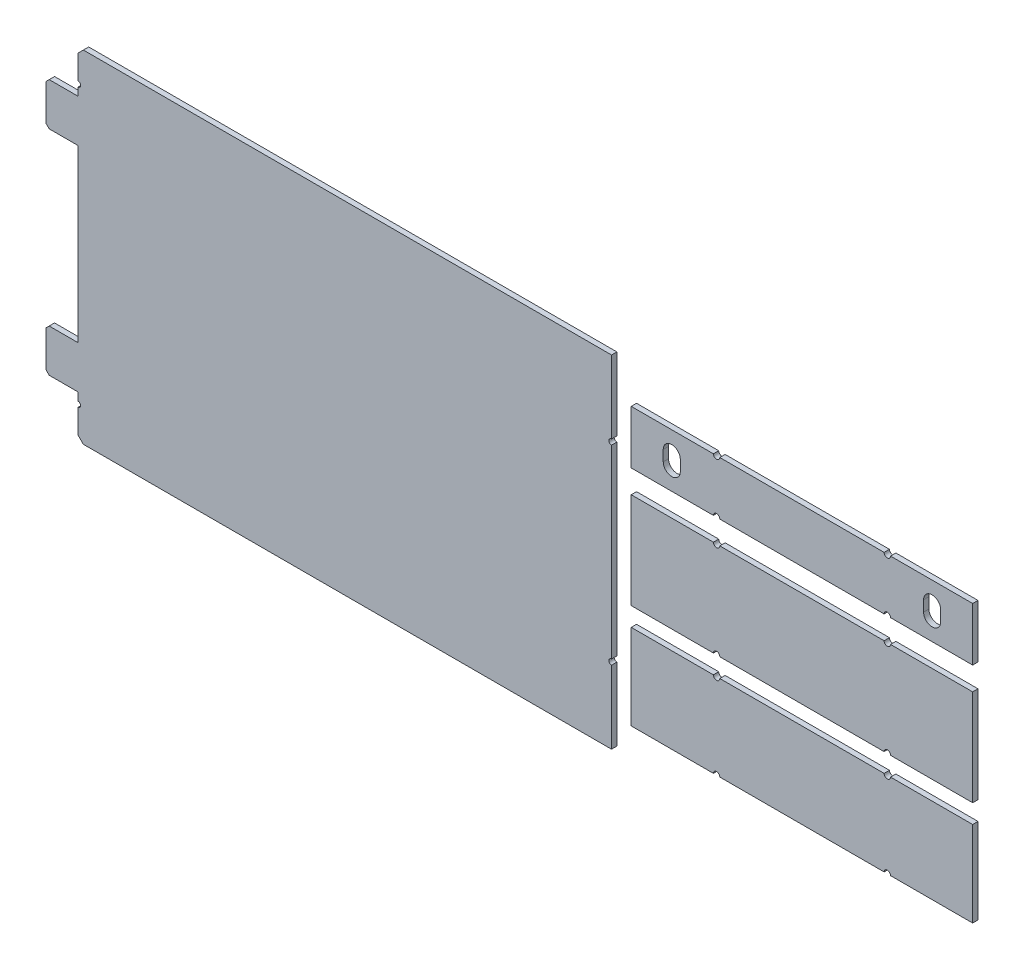
SolidWorks part; units mm, degrees
ref_plane "Ön Düzlem" through (0, 0, 0) normal (0, 0, 1) x (1, 0, 0)
ref_plane "Üst Düzlem" through (0, 0, 0) normal (0, 1, 0) x (1, 0, 0)
ref_plane "Sağ Düzlem" through (0, 0, 0) normal (1, 0, 0) x (0, 0, -1)
sketch "Çizim1" plane through (0, 0, 0) normal (0, 0, 1) x (1, 0, 0)
  line L0 (1992.452, 1746.7533) -> (1992.452, 1712.7533)
  line L1 (1995.452, 1709.7533) -> (2022.452, 1709.7533)
  line L2 (1992.452, 1712.7533) -> (1995.452, 1709.7533)
  line L3 (1995.452, 1749.7533) -> (2022.452, 1749.7533)
  line L4 (1992.452, 1746.7533) -> (1995.452, 1749.7533)
  line L5 (1992.452, 1546.7533) -> (1992.452, 1512.7533)
  line L6 (1995.452, 1509.7533) -> (2022.452, 1509.7533)
  line L7 (1992.452, 1512.7533) -> (1995.452, 1509.7533)
  line L8 (1995.452, 1549.7533) -> (2022.452, 1549.7533)
  line L9 (1992.452, 1546.7533) -> (1995.452, 1549.7533)
  line L10 (2022.452, 1549.7533) -> (2022.452, 1709.7533)
  line L11 (2522.452, 1469.7533) -> (2522.452, 1537.9676)
  line L12 (2522.452, 1542.9676) -> (2522.452, 1716.539)
  line L13 (2522.452, 1721.539) -> (2522.452, 1789.7533)
  line L14 (2027.452, 1469.7533) -> (2522.452, 1469.7533)
  line L15 (2027.452, 1789.7533) -> (2522.452, 1789.7533)
  line L16 (2022.452, 1784.7533) -> (2027.452, 1789.7533)
  line L17 (2022.452, 1749.7533) -> (2022.452, 1757.2533)
  line L18 (2022.452, 1762.2533) -> (2022.452, 1784.7533)
  line L19 (2022.452, 1509.7533) -> (2022.452, 1502.2533)
  line L20 (2022.452, 1497.2533) -> (2022.452, 1474.7533)
  line L21 (2027.452, 1469.7533) -> (2022.452, 1474.7533)
  line L22 (2540.9113, 1497.8976) -> (2540.9113, 1577.8976)
  line L23 (2540.9113, 1577.8976) -> (2617.9113, 1577.8976)
  line L24 (2623.9113, 1577.8976) -> (2777.9113, 1577.8976)
  line L25 (2783.9113, 1577.8976) -> (2860.9113, 1577.8976)
  line L26 (2860.9113, 1577.8976) -> (2860.9113, 1497.8976)
  line L27 (2860.9113, 1497.8976) -> (2783.9113, 1497.8976)
  line L28 (2777.9113, 1497.8976) -> (2623.9113, 1497.8976)
  line L29 (2617.9113, 1497.8976) -> (2540.9113, 1497.8976)
  line L30 (2540.9113, 1595.5433) -> (2540.9113, 1685.5433)
  line L31 (2540.9113, 1685.5433) -> (2617.9113, 1685.5433)
  line L32 (2623.9113, 1685.5433) -> (2777.9113, 1685.5433)
  line L33 (2783.9113, 1685.5433) -> (2860.9113, 1685.5433)
  line L34 (2860.9113, 1685.5433) -> (2860.9113, 1595.5433)
  line L35 (2860.9113, 1595.5433) -> (2783.9113, 1595.5433)
  line L36 (2777.9113, 1595.5433) -> (2623.9113, 1595.5433)
  line L37 (2617.9113, 1595.5433) -> (2540.9113, 1595.5433)
  line L38 (2540.9113, 1707.2753) -> (2540.9113, 1757.2753)
  line L39 (2540.9113, 1757.2753) -> (2617.9113, 1757.2753)
  line L40 (2623.9113, 1757.2753) -> (2777.9113, 1757.2753)
  line L41 (2783.9113, 1757.2753) -> (2860.9113, 1757.2753)
  line L42 (2860.9113, 1757.2753) -> (2860.9113, 1707.2753)
  line L43 (2860.9113, 1707.2753) -> (2783.9113, 1707.2753)
  line L44 (2777.9113, 1707.2753) -> (2623.9113, 1707.2753)
  line L45 (2617.9113, 1707.2753) -> (2540.9113, 1707.2753)
  line L46 (2570.9113, 1727.2753) -> (2570.9113, 1737.2753)
  line L47 (2586.9113, 1727.2753) -> (2586.9113, 1737.2753)
  line L48 (2830.9113, 1727.2753) -> (2830.9113, 1737.2753)
  line L49 (2814.9113, 1727.2753) -> (2814.9113, 1737.2753)
  line L50 (2830.9113, 1727.2753) -> (2830.9113, 1737.2753)
  line L51 (2814.9113, 1727.2753) -> (2814.9113, 1737.2753)
  arc A0 (2022.452, 1757.2533) -> (2022.452, 1762.2533) centre (2022.452, 1759.7533) ccw
  arc A1 (2522.452, 1721.539) -> (2522.452, 1716.539) centre (2522.452, 1719.039) ccw
  arc A2 (2522.452, 1542.9676) -> (2522.452, 1537.9676) centre (2522.452, 1540.4676) ccw
  arc A3 (2022.452, 1497.2533) -> (2022.452, 1502.2533) centre (2022.452, 1499.7533) ccw
  arc A4 (2623.9113, 1497.8976) -> (2617.9113, 1497.8976) centre (2620.9113, 1497.8976) ccw
  arc A5 (2617.9113, 1577.8976) -> (2623.9113, 1577.8976) centre (2620.9113, 1577.8976) ccw
  arc A6 (2783.9113, 1497.8976) -> (2777.9113, 1497.8976) centre (2780.9113, 1497.8976) ccw
  arc A7 (2777.9113, 1577.8976) -> (2783.9113, 1577.8976) centre (2780.9113, 1577.8976) ccw
  arc A8 (2623.9113, 1595.5433) -> (2617.9113, 1595.5433) centre (2620.9113, 1595.5433) ccw
  arc A9 (2617.9113, 1685.5433) -> (2623.9113, 1685.5433) centre (2620.9113, 1685.5433) ccw
  arc A10 (2783.9113, 1595.5433) -> (2777.9113, 1595.5433) centre (2780.9113, 1595.5433) ccw
  arc A11 (2777.9113, 1685.5433) -> (2783.9113, 1685.5433) centre (2780.9113, 1685.5433) ccw
  arc A12 (2623.9113, 1707.2753) -> (2617.9113, 1707.2753) centre (2620.9113, 1707.2753) ccw
  arc A13 (2617.9113, 1757.2753) -> (2623.9113, 1757.2753) centre (2620.9113, 1757.2753) ccw
  arc A14 (2783.9113, 1707.2753) -> (2777.9113, 1707.2753) centre (2780.9113, 1707.2753) ccw
  arc A15 (2777.9113, 1757.2753) -> (2783.9113, 1757.2753) centre (2780.9113, 1757.2753) ccw
  arc A16 (2586.9113, 1737.2753) -> (2570.9113, 1737.2753) centre (2578.9113, 1737.2753) ccw
  arc A17 (2570.9113, 1727.2753) -> (2586.9113, 1727.2753) centre (2578.9113, 1727.2753) ccw
  arc A18 (2830.9113, 1737.2753) -> (2814.9113, 1737.2753) centre (2822.9113, 1737.2753) ccw
  arc A19 (2814.9113, 1727.2753) -> (2830.9113, 1727.2753) centre (2822.9113, 1727.2753) ccw
  arc A20 (2830.9113, 1737.2753) -> (2814.9113, 1737.2753) centre (2822.9113, 1737.2753) ccw
  arc A21 (2814.9113, 1727.2753) -> (2830.9113, 1727.2753) centre (2822.9113, 1727.2753) ccw
  point P0 (2822.9113, 1745.2753)
  point P1 (2822.9113, 1719.2753)
  dimension "D1" = 320
  dimension "D2" = 530
  dimension "D3" = 320
  dimension "D4" = 50
  dimension "D5" = 42
  dimension "D6" = 80
  dimension "D7" = 160
  dimension "D8" = 80
  dimension "D9" = 90
  dimension "D10" = 80
  dimension "D11" = 26
  dimension "D12" = 16
  dimension "D13" = 244
extrude "Yükseklik-Ekstrüzyon1" add sketch "Çizim1" along normal blind 5 contours A3 L20 L21 L14 L11 A2 L12 A1 L13 L15 L16 L18 A0 L17 L3 L4 L0 L2 L1 L10 L8 L9 L5 L7 L6 L19 | A15 L40 A13 L39 L38 L45 A12 L44 A14 L43 L42 L41 A19 L49 A18 L48 A17 L46 A16 L47 | A11 L32 A9 L31 L30 L37 A8 L36 A10 L35 L34 L33 | A7 L24 A5 L23 L22 L29 A4 L28 A6 L27 L26 L25
